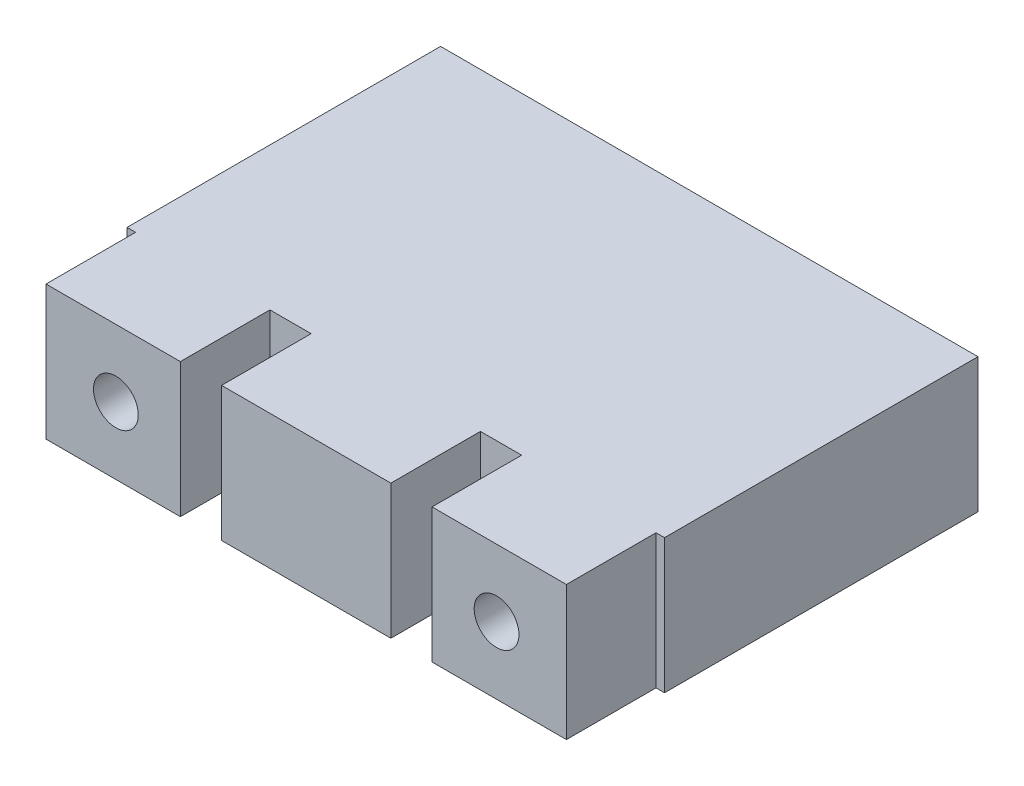
SolidWorks part; units mm, degrees
ref_plane "Front Plane" through (0, 0, 0) normal (0, 0, 1) x (1, 0, 0)
ref_plane "Top Plane" through (0, 0, 0) normal (0, 1, 0) x (1, 0, 0)
ref_plane "Right Plane" through (0, 0, 0) normal (1, 0, 0) x (0, 0, -1)
sketch "Sketch1" plane through (0, 0, 0) normal (0, 0, 1) x (1, 0, 0)
  line L1 (0, 9.525) -> (12.0015, 9.525)
  line L2 (0, 9.525) -> (0, 0)
  line L3 (0, 0) -> (12.0015, 0)
  line L4 (12.0015, 9.525) -> (12.0015, 0)
  dimension "D1" = 12.0015
  dimension "D2" = 9.525
sketch "Sketch2" plane through (0, 0, 0) normal (0, 0, 1) x (1, 0, 0)
  line L0 (0, 9.525) -> (12.0015, 9.525) construction
  line L1 (-2.921, 9.525) -> (-12.446, 9.525)
  line L2 (-2.921, 9.525) -> (-2.921, 0)
  line L3 (-2.921, 0) -> (-12.446, 0)
  line L4 (-12.446, 9.525) -> (-12.446, 0)
  line L5 (0, 0) -> (12.0015, 0) construction
  line L6 (0, 9.525) -> (0, 0) construction
  line L7 (-12.446, 4.7625) -> (-2.921, 4.7625) construction
  circle A0 centre (-7.493, 4.7625) radius 1.5875
  point P10 (-7.493, 4.7625)
  dimension "D4" = 3.175
  dimension "D1" = 2.921
  dimension "D2" = 9.525
  dimension "D3" = 4.572
extrude "Boss-Extrude3" add sketch "Sketch1" against normal blind 6.35 separate body contours L4 L3 L2 L1
ref_plane "Plane1" through (12.0015, 9.525, -6.35) normal (1, 0, 0) x (0, 0, -1)
sketch "Sketch4" plane through (0, 0, -6.35) normal (0, 0, -1) x (-1, 0, 0)
  line L0 (0, 9.525) -> (-12.0015, 0) construction
  line L1 (13.0493, 9.525) -> (-25.0507, 9.525)
  line L2 (13.0493, 9.525) -> (13.0493, 0)
  line L3 (13.0493, 0) -> (-25.0507, 0)
  line L4 (-25.0507, 9.525) -> (-25.0507, 0)
  line L5 (0, 9.525) -> (-12.0015, 9.525) construction
  line L6 (0, 0) -> (-12.0015, 0) construction
  line L8 (-12.0015, 9.525) -> (0, 0) construction
  line L9 (-6.0007, 4.7625) -> (-6.0007, 0) construction
  point P16 (-6.0007, 4.7625)
  dimension "D1" = 38.1
extrude "Boss-Extrude4" add sketch "Sketch4" along normal blind 22.225
extrude "Boss-Extrude5" add sketch "Sketch2" against normal up to next (6.35 mm away)
ref_plane "Plane2" through (6.0007, 0, 0) normal (1, 0, 0) x (0, 0, -1)
mirror "Mirror8" about plane through (6.0007, 0, 0) normal (1, 0, 0) of "Boss-Extrude5"
